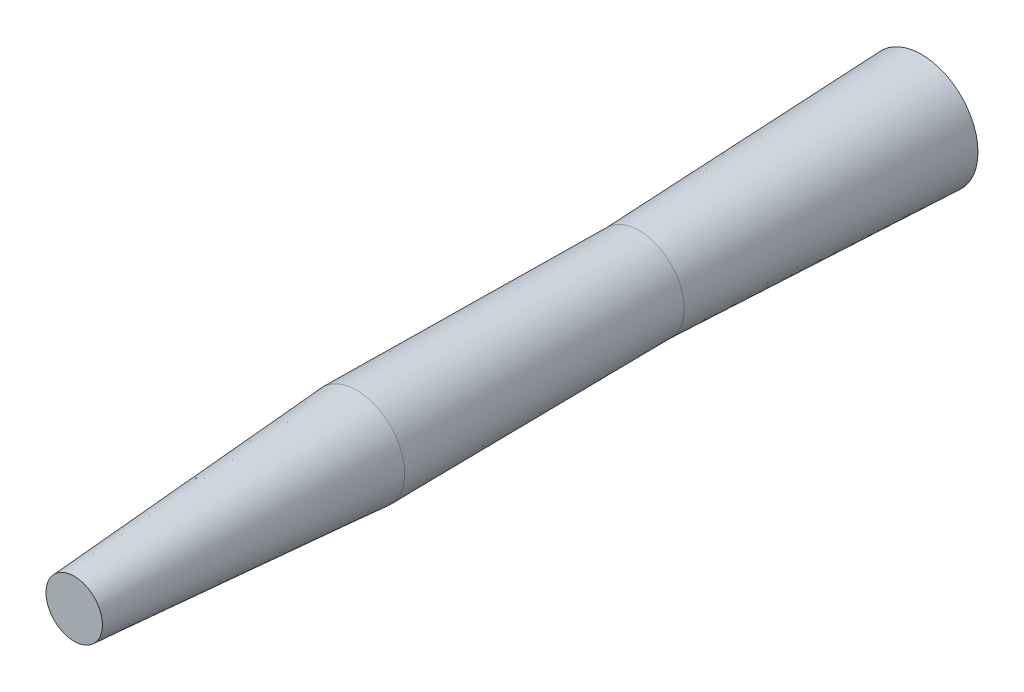
SolidWorks part; units mm, degrees
ref_plane "Front Plane" through (0, 0, 0) normal (0, 0, 1) x (1, 0, 0)
ref_plane "Top Plane" through (0, 0, 0) normal (0, 1, 0) x (1, 0, 0)
ref_plane "Right Plane" through (0, 0, 0) normal (1, 0, 0) x (0, 0, -1)
sketch "Sketch1" plane through (0, 0, 0) normal (0, 0, 1) x (1, 0, 0)
  circle A0 centre (0, 0) radius 20
ref_plane "Plane1" through (0, 0, 100) normal (0, 0, 1) x (1, 0, 0)
sketch "Sketch2" plane through (0, 0, 100) normal (0, 0, 1) x (1, 0, 0)
  circle A0 centre (0, 0) radius 16
loft "Loft1" add profiles "Sketch1", "Sketch2"
ref_plane "Plane2" through (0, 0, 200) normal (0, 0, 1) x (1, 0, 0)
sketch "Sketch3" plane through (0, 0, 200) normal (0, 0, 1) x (1, 0, 0)
  circle A0 centre (0, 0) radius 17
loft "Loft4" add profiles "Sketch3" section edge at (16, 0, 100) section "Sketch3"
ref_plane "Plane3" through (0, 0, 300) normal (0, 0, 1) x (1, 0, 0)
sketch "Sketch4" plane through (0, 0, 300) normal (0, 0, 1) x (1, 0, 0)
  circle A0 centre (0, 0) radius 10
loft "Loft5" add profiles "Sketch4" section edge at (17, 0, 200) section "Sketch4"
